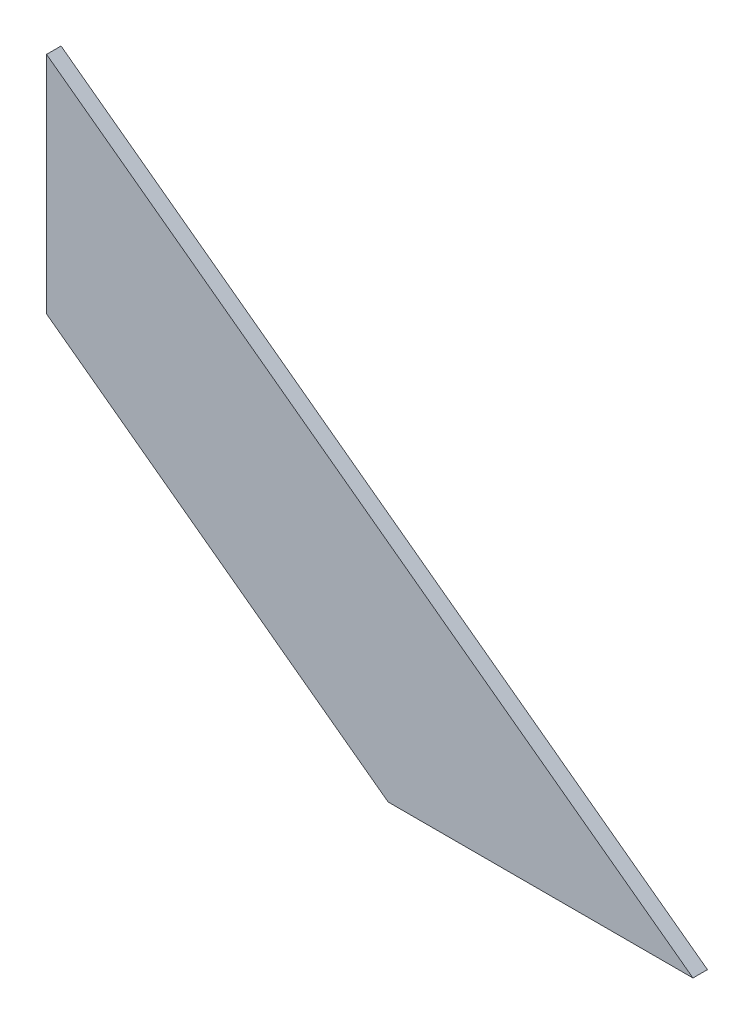
SolidWorks part; units mm, degrees
ref_plane "Front Plane" through (0, 0, 0) normal (0, 0, 1) x (1, 0, 0)
ref_plane "Top Plane" through (0, 0, 0) normal (0, 1, 0) x (1, 0, 0)
ref_plane "Right Plane" through (0, 0, 0) normal (1, 0, 0) x (0, 0, -1)
sketch "Sketch4" plane through (0, 0, 0) normal (0, 0, -1) x (-1, 0, 0)
  line L10 (471.2925, -20.0348) -> (539.3625, 30.1622)
  line L11 (539.3625, 30.1622) -> (539.3625, 6.4926)
  line L12 (539.3625, 6.4926) -> (503.3899, -20.0348)
  line L13 (503.3899, -20.0348) -> (471.2925, -20.0348)
  line L14 (564.1807, -20.0348) -> (459.4057, -20.0348) construction
  line L15 (546.4745, -17.0828) -> (546.4745, 32.4172) construction
  line L17 (446.7057, -37.2467) -> (564.1807, -37.2467) construction
  dimension "D1" = 19.05
  dimension "D2" = 7.112
  dimension "D3" = 32.0973
  dimension "D4" = 17.2118
extrude "Boss-Extrude1" add sketch "Sketch4" along normal blind 1.524
